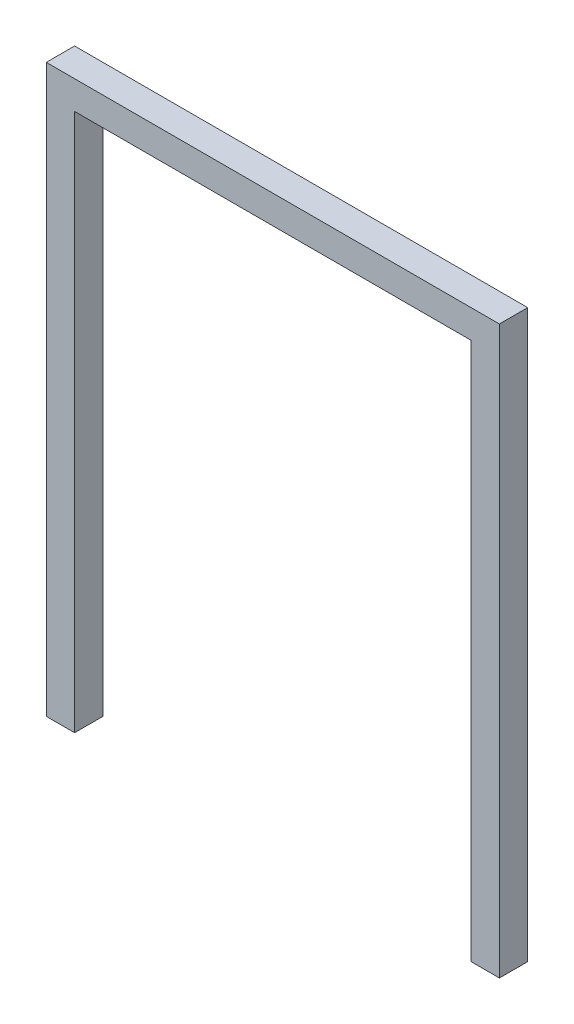
SolidWorks part; units mm, degrees
ref_plane "Front Plane" through (0, 0, 0) normal (0, 0, 1) x (1, 0, 0)
ref_plane "Top Plane" through (0, 0, 0) normal (0, 1, 0) x (1, 0, 0)
ref_plane "Right Plane" through (0, 0, 0) normal (1, 0, 0) x (0, 0, -1)
sketch "Sketch2" plane through (0, 0, 0) normal (0, 0, 1) x (1, 0, 0)
  line L0 (25.4, 482.6) -> (381, 482.6)
  line L1 (0, 0) -> (25.4, 0)
  line L2 (0, 0) -> (0, 508)
  line L3 (0, 508) -> (406.4, 508)
  line L4 (406.4, 0) -> (406.4, 508)
  line L5 (381, 25.4) -> (381, 482.6)
  line L7 (25.4, 25.4) -> (25.4, 482.6)
  line L8 (25.4, 25.4) -> (381, 25.4) construction
  line L9 (25.4, 25.4) -> (25.4, 0)
  line L10 (381, 25.4) -> (381, 0)
  line L11 (381, 0) -> (406.4, 0)
  line L12 (0, 0) -> (406.4, 0) construction
  dimension "D1" = 508
  dimension "D2" = 355.6
  dimension "D3" = 25.4
extrude "Boss-Extrude1" add sketch "Sketch2" along normal blind 25.4
